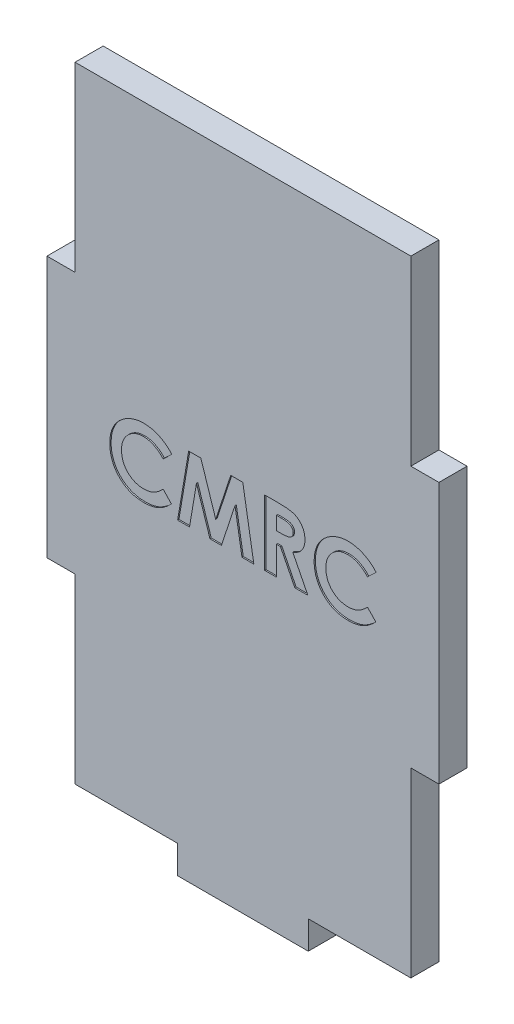
SolidWorks part; units mm, degrees
ref_plane "Plan de face" through (0, 0, 0) normal (0, 0, 1) x (1, 0, 0)
ref_plane "Plan de dessus" through (0, 0, 0) normal (0, 1, 0) x (1, 0, 0)
ref_plane "Plan de droite" through (0, 0, 0) normal (1, 0, 0) x (0, 0, -1)
sketch "Sketch1" plane through (0, 0, 0) normal (0, 0, 1) x (1, 0, 0)
  line L0 (-32.639, -25.4) -> (-32.639, -60.7695)
  line L1 (-32.639, 60.7695) -> (32.639, 60.7695)
  line L2 (-32.639, 60.7695) -> (-32.639, 25.4)
  line L3 (-32.639, -60.7695) -> (-12.7, -60.7695)
  line L5 (-32.639, 60.7695) -> (0, 0) construction
  line L6 (-32.639, -60.7695) -> (0, 0) construction
  line L16 (-12.7, -60.7695) -> (-12.7, -66.2305)
  line L17 (-12.7, -66.2305) -> (12.7, -66.2305)
  line L19 (0, 60.7695) -> (0, -66.2305) construction
  line L20 (38.1, 0) -> (-38.1, 0) construction
  line L21 (-32.639, 25.4) -> (-38.1, 25.4)
  line L23 (-32.639, -25.4) -> (-38.1, -25.4)
  line L24 (-38.1, 25.4) -> (-38.1, -25.4)
  line L26 (32.639, -60.7695) -> (0, 0) construction
  line L31 (32.639, 60.7695) -> (0, 0) construction
  line L32 (38.1, 25.4) -> (38.1, -25.4)
  line L34 (32.639, -25.4) -> (38.1, -25.4)
  line L35 (32.639, 25.4) -> (38.1, 25.4)
  line L36 (12.7, -60.7695) -> (12.7, -66.2305)
  line L37 (32.639, -60.7695) -> (12.7, -60.7695)
  line L38 (32.639, 60.7695) -> (32.639, 25.4)
  line L39 (32.639, -25.4) -> (32.639, -60.7695)
  point P0 (0, 0)
  dimension "D5" = 5.461
  dimension "D7" = 50.8
  dimension "D3" = 5.461
  dimension "D4" = 25.4
  dimension "D6" = 76.2
  dimension "D1" = 127
extrude "Boss-Extrude1" add sketch "Sketch1" along normal mid plane 5.461
sketch "Sketch2" plane through (0, 0, 2.7305) normal (0, 0, 1) x (1, 0, 0)
  line L0 (-38.1, -6.35) -> (38.1, -6.35) construction
  line L1 (0, 0) -> (0, -6.35) construction
  text T0 "CMRC" font "Century Gothic" height 12.7
  point P2 (0, -6.35)
  dimension "D1" = 6.35
  dimension "D2" = 76.2
extrude "Cut-Extrude1" cut sketch "Sketch2" against normal blind 0.254
equation "\"vee_block_width\" = 3in"
equation "\"material_thickness\" = 0.215in"
equation "\"D5@Sketch1\"=\"material_thickness\""
equation "\"D3@Sketch1\"=\"material_thickness\""
equation "\"D6@Sketch1\"= \"vee_block_width\""
equation "\"D1@Sketch1\"=5"
equation "\"D4@Sketch1\"=1"
equation "\"D1@Sketch2\"=0.25"
equation "\"D1@Boss-Extrude1\"=\"material_thickness\""
